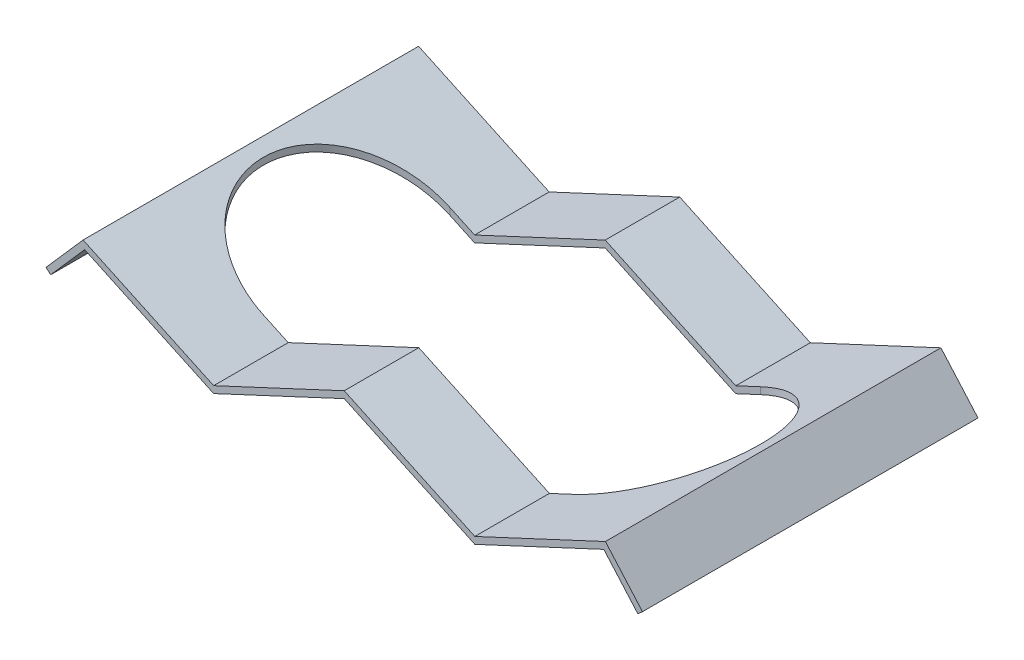
SolidWorks part; units mm, degrees
ref_plane "Plan de face" through (0, 0, 0) normal (0, 0, 1) x (1, 0, 0)
ref_plane "Plan de dessus" through (0, 0, 0) normal (0, 1, 0) x (1, 0, 0)
ref_plane "Plan de droite" through (0, 0, 0) normal (1, 0, 0) x (0, 0, -1)
sketch "Esquisse1" plane through (0, 0, 0) normal (0, 0, 1) x (1, 0, 0)
  line L0 (-24, 2.45) -> (-24, -2.45) construction
  line L1 (-24, -2.45) -> (24, -2.45) construction
  line L2 (24, -2.45) -> (24, 2.45) construction
  line L3 (24, 2.45) -> (-24, 2.45) construction
  line L4 (0, -55) -> (0, 55) construction
  line L5 (55, 0) -> (-55, 0) construction
  line L6 (-24, -0.95) -> (-21.0162, 2.45)
  line L7 (-21.0162, 2.45) -> (-10.5081, -2.45)
  line L8 (-10.5081, -2.45) -> (0, 2.45)
  line L9 (0, 2.45) -> (10.5081, -2.45)
  line L10 (10.5081, -2.45) -> (21.0162, 2.45)
  line L11 (21.0162, 2.45) -> (24, -0.95)
  point P4 (0, 2.45)
  point P7 (-24, 0)
  point P17 (-21.0162, 2.45)
  point P18 (-21.0162, 2.45)
  point P19 (0, 0)
  dimension "D1" = 48
  dimension "D2" = 4.9
  dimension "D3" = 1.5
  dimension "D4" = 130
  dimension "D5" = 1.5
extrude "Extru.-Mince1" add sketch "Esquisse1" along normal mid plane 27 thin
sketch "Esquisse2" plane through (0, 0, 0) normal (0, 1, 0) x (1, 0, 0)
  line L0 (-12.5, 0) -> (12.5, 0) construction
  line L1 (-2.9984, 0) -> (2.9984, 0) construction
  line L2 (-12.5, 7.5) -> (12.5, 7.5)
  line L3 (-12.5, -7.5) -> (12.5, -7.5)
  line L4 (0, -2.9984) -> (0, 2.9984) construction
  arc A0 (-12.5, 7.5) -> (-12.5, -7.5) centre (-12.5, 0) ccw
  arc A1 (12.5, -7.5) -> (12.5, 7.5) centre (12.5, 0) ccw
  point P5 (0, 0)
  point P10 (0, 0)
  point P13 (-20, 0)
  point P14 (20, 0)
  dimension "D1" = 40
  dimension "D2" = 15
extrude "Enlèv. mat.-Extru.1" cut sketch "Esquisse2" against normal through all and the other way through all
